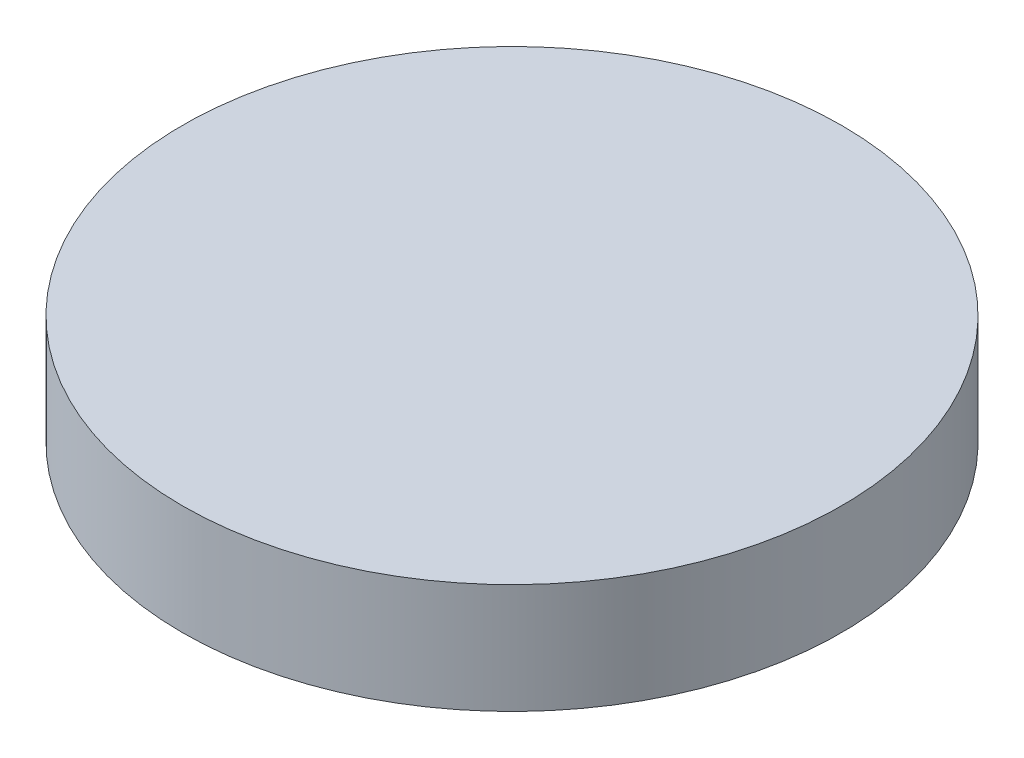
SolidWorks part; units mm, degrees
material "AISI Type 316L stainless steel"
ref_plane "Front Plane" through (0, 0, 0) normal (0, 0, 1) x (1, 0, 0)
ref_plane "Top Plane" through (0, 0, 0) normal (0, 1, 0) x (1, 0, 0)
ref_plane "Right Plane" through (0, 0, 0) normal (1, 0, 0) x (0, 0, -1)
sketch "Sketch1" plane through (0, 0, 0) normal (0, 1, 0) x (1, 0, 0)
  circle A0 centre (0, 0) radius 30
  dimension "D1" = 60
extrude "Boss-Extrude1" add sketch "Sketch1" along normal blind 10
